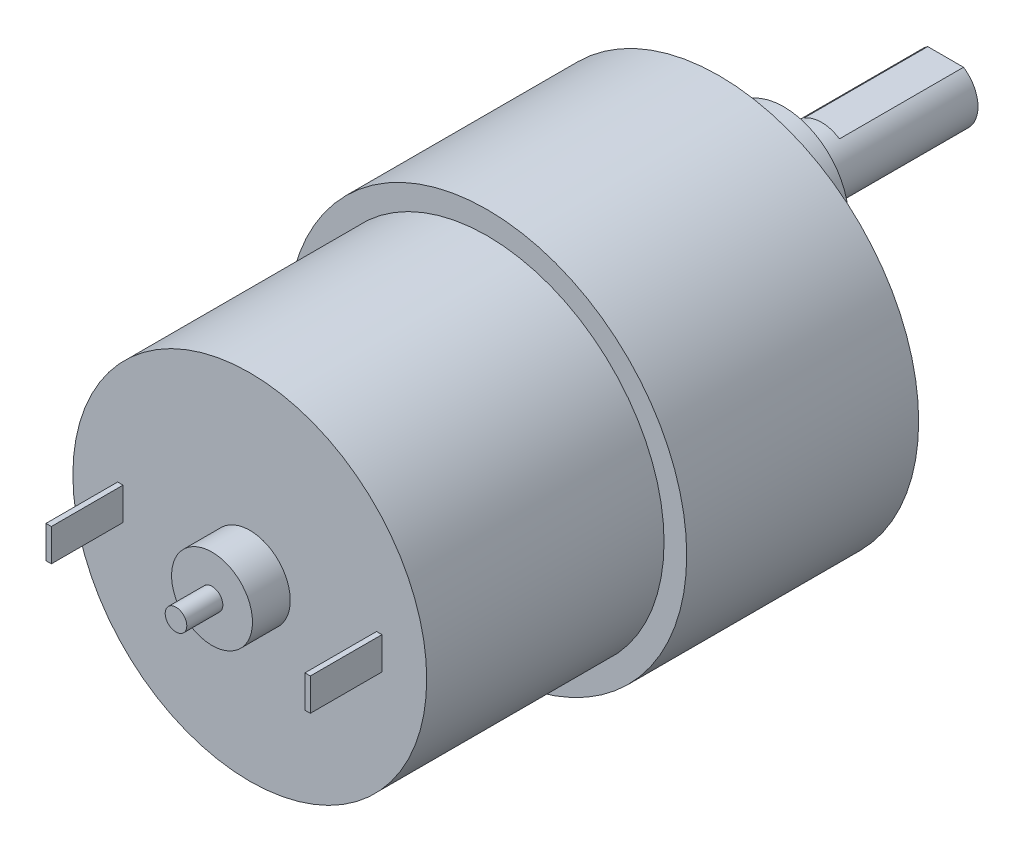
SolidWorks part; units mm, degrees
ref_plane "前视基准面" through (0, 0, 0) normal (0, 0, 1) x (1, 0, 0)
ref_plane "上视基准面" through (0, 0, 0) normal (0, 1, 0) x (1, 0, 0)
ref_plane "右视基准面" through (0, 0, 0) normal (1, 0, 0) x (0, 0, -1)
sketch "草图1" plane through (0, 0, 0) normal (0, 0, 1) x (1, 0, 0)
  circle A0 centre (0, 0) radius 18.5
  dimension "D1" = 37
extrude "凸台-拉伸1" add sketch "草图1" along normal blind 21.5
sketch "草图2" plane through (0, 0, 0) normal (0, 0, -1) x (-1, 0, 0)
  circle A0 centre (0, 7) radius 6
  dimension "D1" = 12
  dimension "D2" = 7
extrude "凸台-拉伸2" add sketch "草图2" along normal blind 6
sketch "草图3" plane through (0, 0, -6) normal (0, 0, -1) x (-1, 0, 0)
  circle A0 centre (0, 7) radius 3
  dimension "D1" = 6
extrude "凸台-拉伸3" add sketch "草图3" along normal blind 15
sketch "草图4" plane through (0, 0, -21) normal (0, 0, -1) x (-1, 0, 0)
  line L0 (-1.6583, 9.5) -> (1.6583, 9.5)
  circle A0 centre (0, 7) radius 3 construction
  circle A1 centre (0, 7) radius 3 construction
  dimension "D1" = 2.5
extrude "切除-拉伸1" cut sketch "草图4" against normal blind 11.5 and the other way through all
sketch "草图5" plane through (0, 0, 0) normal (0, 0, -1) x (-1, 0, 0)
  circle A0 centre (0, 0) radius 15.5 construction
  circle A1 centre (15.5, 0) radius 1.5
  circle A2 centre (7.75, -13.4234) radius 1.5
  circle A3 centre (-7.75, -13.4234) radius 1.5
  circle A4 centre (-15.5, 0) radius 1.5
  circle A5 centre (-7.75, 13.4234) radius 1.5
  circle A6 centre (7.75, 13.4234) radius 1.5
  point P17 (0, 0)
  dimension "D1" = 31
  dimension "D2" = 3
  dimension "D4" = 15.5
  dimension "D5" = 13.4234
  dimension "D3" = 6
extrude "切除-拉伸2" cut sketch "草图5" against normal blind 5
sketch "草图6" plane through (0, 0, 21.5) normal (0, 0, 1) x (1, 0, 0)
  circle A0 centre (0, 0) radius 16.4
  dimension "D1" = 32.8
extrude "凸台-拉伸4" add sketch "草图6" along normal blind 22
sketch "草图7" plane through (0, 0, 43.5) normal (0, 0, 1) x (1, 0, 0)
  circle A0 centre (0, 0) radius 1
  dimension "D1" = 2
extrude "凸台-拉伸5" add sketch "草图7" along normal blind 6.84
sketch "草图8" plane through (0, 0, 43.5) normal (0, 0, 1) x (1, 0, 0)
  circle A0 centre (0, 0) radius 3.75
  dimension "D1" = 7.5
extrude "凸台-拉伸6" add sketch "草图8" along normal blind 3.5
sketch "草图9" plane through (0, 0, 43.5) normal (0, 0, 1) x (1, 0, 0)
  line L0 (0, 0) -> (0, 10.6569) construction
  line L1 (-12.25, 1.5) -> (-11.75, 1.5)
  line L2 (-12.25, 1.5) -> (-12.25, -1.5)
  line L3 (-12.25, -1.5) -> (-11.75, -1.5)
  line L4 (-11.75, 1.5) -> (-11.75, -1.5)
  line L5 (-12.25, 1.5) -> (-11.75, -1.5) construction
  line L6 (-12.25, -1.5) -> (-11.75, 1.5) construction
  line L11 (12.25, -1.5) -> (11.75, 1.5) construction
  line L12 (12.25, 1.5) -> (11.75, -1.5) construction
  line L13 (11.75, 1.5) -> (11.75, -1.5)
  line L14 (12.25, -1.5) -> (11.75, -1.5)
  line L15 (12.25, 1.5) -> (12.25, -1.5)
  line L16 (12.25, 1.5) -> (11.75, 1.5)
  point P0 (-12, 0)
  point P9 (12, 0)
  dimension "D1" = 0.5
  dimension "D2" = 3
  dimension "D3" = 24
extrude "凸台-拉伸7" add sketch "草图9" along normal blind 6.64
